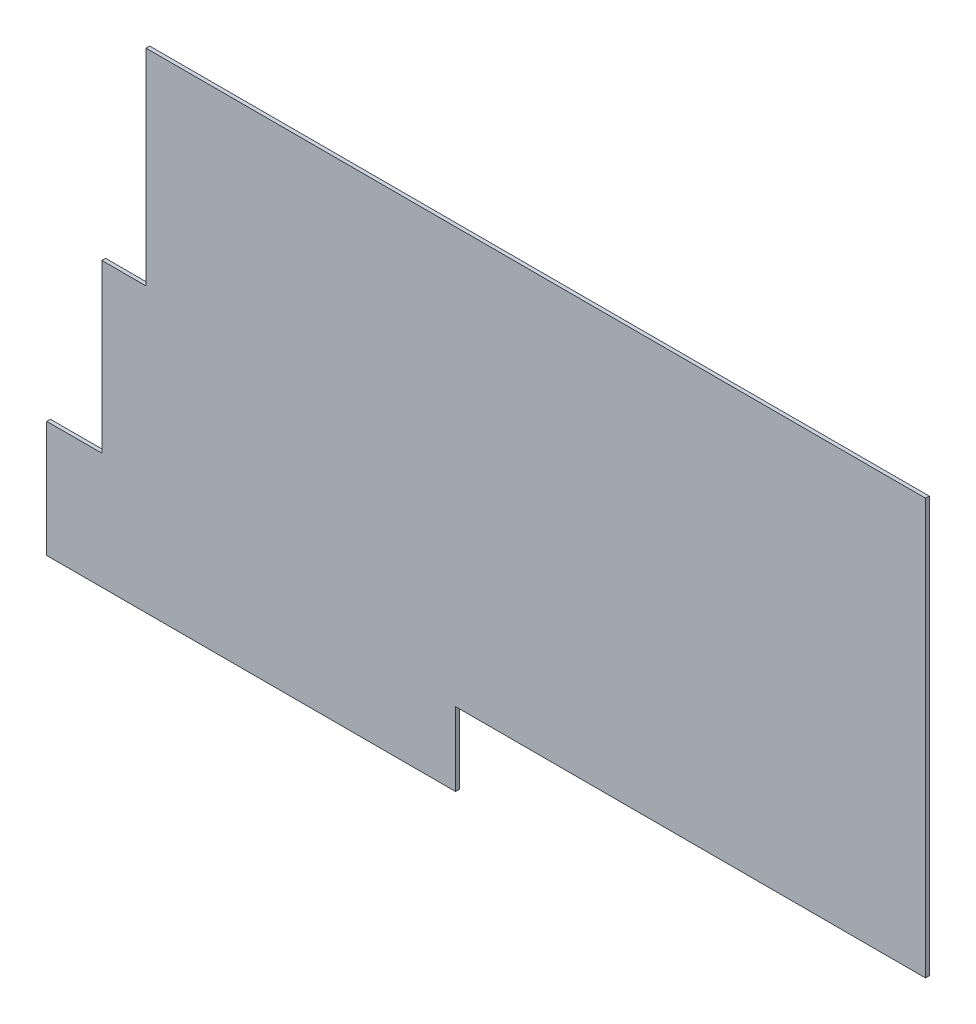
SolidWorks part; units mm, degrees
ref_plane "Front Plane" through (0, 0, 0) normal (0, 0, 1) x (1, 0, 0)
ref_plane "Top Plane" through (0, 0, 0) normal (0, 1, 0) x (1, 0, 0)
ref_plane "Right Plane" through (0, 0, 0) normal (1, 0, 0) x (0, 0, -1)
sketch "Sketch1" plane through (0, 0, 0) normal (0, 0, 1) x (1, 0, 0)
  line L0 (8530, -2750) -> (2140, -2750)
  line L1 (-2070, 2900) -> (8530, 2900)
  line L2 (-3420, -3750) -> (2140, -3750)
  line L3 (8530, 2900) -> (8530, -2750)
  line L4 (2140, -2750) -> (2140, -3750)
  line L5 (-2070, 2900) -> (-2070, 100)
  line L6 (-2070, 100) -> (-2670, 100)
  line L7 (-2670, 100) -> (-2670, -2170)
  line L8 (-2670, -2170) -> (-3420, -2170)
  line L9 (0, 4705.3253) -> (0, -4658.5586) construction
  line L10 (8916.2265, 0) -> (-4562.9089, 0) construction
  line L11 (-3420, -2170) -> (-3420, -3750)
  dimension "D1" = 10600
  dimension "D2" = 8530
  dimension "D3" = 5070
  dimension "D4" = 6650
  dimension "D5" = 5650
  dimension "D6" = 2750
  dimension "D7" = 6390
  dimension "D8" = 750
  dimension "D9" = 1350
  dimension "D10" = 2800
extrude "Extrude1" add sketch "Sketch1" along normal blind 50
ref_plane "Plane3" through (-5000, 0, 0) normal (1, 0, 0) x (0, 0, -1)
ref_plane "Plane4" through (-4480, 0, 0) normal (1, 0, 0) x (0, 0, -1)
sketch "Sketch2" plane through (-5000, 0, 0) normal (1, 0, 0) x (0, 0, -1)
  line L0 (0, -2750) -> (0, 2900) construction
  line L1 (855, 2650) -> (855, -1397.8432) construction
  circle A0 centre (855, 2650) radius 175
  circle A1 centre (855, -825) radius 298.0285
  dimension "D3" = 350
  dimension "D1" = 855
  dimension "D2" = 2650
  dimension "D4" = 825
